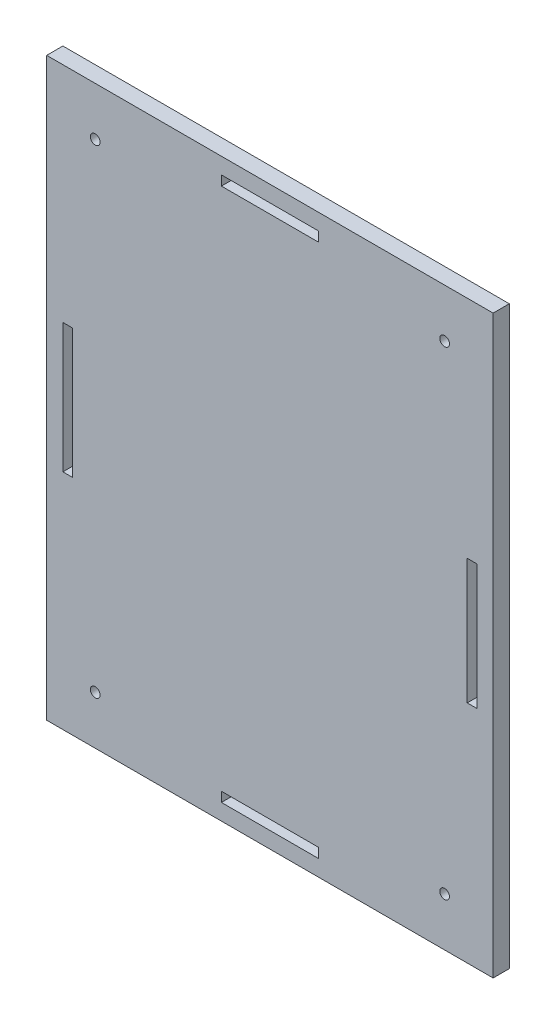
SolidWorks part; units mm, degrees
ref_plane "Front Plane" through (0, 0, 0) normal (0, 0, 1) x (1, 0, 0)
ref_plane "Top Plane" through (0, 0, 0) normal (0, 1, 0) x (1, 0, 0)
ref_plane "Right Plane" through (0, 0, 0) normal (1, 0, 0) x (0, 0, -1)
sketch "Sketch2" plane through (0, 0, 0) normal (0, 0, 1) x (1, 0, 0)
  line L1 (69, -89) -> (-69, -89)
  line L2 (69, -89) -> (69, 89)
  line L3 (69, 89) -> (-69, 89)
  line L4 (-69, -89) -> (-69, 89)
  line L5 (69, -89) -> (-69, 89) construction
  line L6 (69, 89) -> (-69, -89) construction
  point P0 (0, 0)
  dimension "D1" = 178
  dimension "D2" = 138
extrude "Boss-Extrude1" add sketch "Sketch2" along normal blind 5
sketch "Sketch3" plane through (0, 0, 5) normal (0, 0, 1) x (1, 0, 0)
  line L1 (-15, 84) -> (15, 84)
  line L2 (-15, 84) -> (-15, 81)
  line L3 (-15, 81) -> (15, 81)
  line L4 (15, 84) -> (15, 81)
  line L5 (-15, 84) -> (15, 81) construction
  line L6 (-15, 81) -> (15, 84) construction
  line L11 (69, 89) -> (-69, 89) construction
  point P0 (0, 82.5)
  point P8 (0, 89)
  point P10 (0, 84)
  dimension "D1" = 0
  dimension "D2" = 5
  dimension "D3" = 3
extrude "Cut-Extrude1" cut sketch "Sketch3" against normal through all
sketch "Sketch4" plane through (0, 0, 5) normal (0, 0, 1) x (1, 0, 0)
  line L1 (-15, -81) -> (15, -81)
  line L2 (-15, -81) -> (-15, -84)
  line L3 (-15, -84) -> (15, -84)
  line L4 (15, -81) -> (15, -84)
  line L5 (-15, -81) -> (15, -84) construction
  line L6 (-15, -84) -> (15, -81) construction
  line L8 (-69, -89) -> (69, -89) construction
  point P0 (0, -82.5)
  point P7 (0, -89)
  point P8 (0, -84)
  dimension "D1" = 0
  dimension "D2" = 3
  dimension "D3" = 5
sketch "Sketch5" plane through (0, 0, 5) normal (0, 0, 1) x (1, 0, 0)
  line L1 (-64, 20) -> (-61, 20)
  line L2 (-64, 20) -> (-64, -20)
  line L3 (-64, -20) -> (-61, -20)
  line L4 (-61, 20) -> (-61, -20)
  line L5 (-64, 20) -> (-61, -20) construction
  line L6 (-64, -20) -> (-61, 20) construction
  line L7 (-69, 89) -> (-69, -89) construction
  point P0 (-62.5, 0)
  point P7 (-69, 0)
  point P8 (-64, 0)
  dimension "D1" = 0
  dimension "D2" = 3
  dimension "D3" = 5
sketch "Sketch6" plane through (0, 0, 5) normal (0, 0, 1) x (1, 0, 0)
  line L1 (61, 19.3548) -> (64, 19.3548)
  line L2 (61, 19.3548) -> (61, -19.3548)
  line L3 (61, -19.3548) -> (64, -19.3548)
  line L4 (64, 19.3548) -> (64, -19.3548)
  line L5 (61, 19.3548) -> (64, -19.3548) construction
  line L6 (61, -19.3548) -> (64, 19.3548) construction
  line L8 (-69, -89) -> (69, -89) construction
  line L10 (69, -89) -> (69, 89) construction
  point P0 (64, 0)
  point P6 (62.5, 0)
  dimension "D1" = 89
  dimension "D2" = 5
  dimension "D3" = 3
extrude "Cut-Extrude2" cut sketch "Sketch4" against normal blind 8
extrude "Cut-Extrude3" cut sketch "Sketch6" against normal blind 8
extrude "Cut-Extrude4" cut sketch "Sketch5" against normal blind 8
sketch "Sketch8" plane through (0, 0, 5) normal (0, 0, 1) x (1, 0, 0)
  line L0 (69, 89) -> (-69, 89) construction
  line L2 (69, -89) -> (69, 89) construction
  line L6 (-69, 89) -> (-69, -89) construction
  line L8 (-69, -89) -> (69, -89) construction
  line L11 (69, 89) -> (-69, 89) construction
  circle A0 centre (54, -74) radius 1.5
  circle A1 centre (54, 74) radius 1.5
  circle A2 centre (-54, 74) radius 1.5
  circle A3 centre (-54, -74) radius 1.5
  dimension "D1" = 3
  dimension "D4" = 3
  dimension "D6" = 3
  dimension "D10" = 15
  dimension "D2" = 15
  dimension "D3" = 2
  dimension "D5" = 15
  dimension "D7" = 15
  dimension "D8" = 15
  dimension "D9" = 15
  dimension "D11" = 15
  dimension "D12" = 15
extrude "Cut-Extrude5" cut sketch "Sketch8" against normal through all
